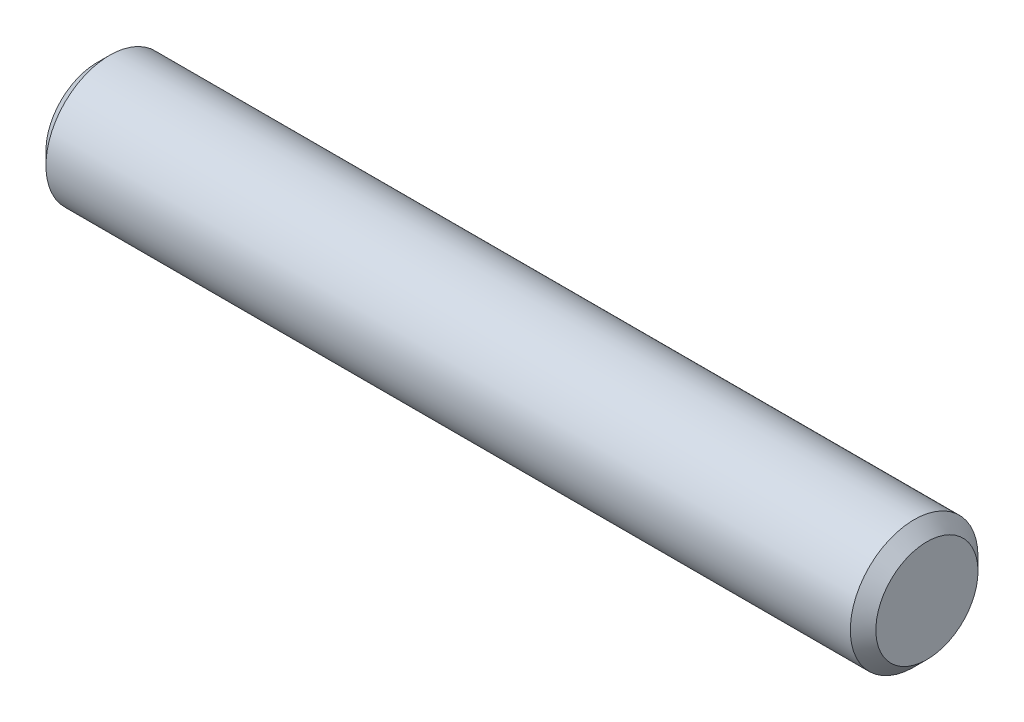
SolidWorks part; units mm, degrees
ref_plane "Front" through (0, 0, 0) normal (0, 0, 1) x (1, 0, 0)
ref_plane "Top" through (0, 0, 0) normal (0, 1, 0) x (1, 0, 0)
ref_plane "Right" through (0, 0, 0) normal (1, 0, 0) x (0, 0, -1)
sketch "Sketch1" plane through (0, 0, 0) normal (0, 0, 1) x (1, 0, 0)
  line L0 (-20.6375, 0) -> (20.6375, 0) construction
  line L1 (20.6375, 3.175) -> (20.6375, -3.175) construction
  line L2 (-20.6375, 3.175) -> (-20.6375, -3.175) construction
  dimension "Length" = 41.275
  dimension "Diameter" = 6.35
sketch "Sketch2" plane through (0, 0, 0) normal (1, 0, 0) x (0, 0, -1)
  circle A0 centre (0, 0) radius 3.175
extrude "Extrude1" add sketch "Sketch2" against normal up to vertex (20.6375 mm away) and the other way up to vertex (20.6375 mm away) up to point (-20.6375, 3.175, 0) other way up to point (20.6375, 3.175, 0)
chamfer "Chamfer1" distance 0.635 angle 45 2 edges at (20.6375, 0, -3.175) (-20.6375, 0, -3.175)
equation "\"D1@Chamfer1\" = \"Diameter@Sketch1\"*.1"
